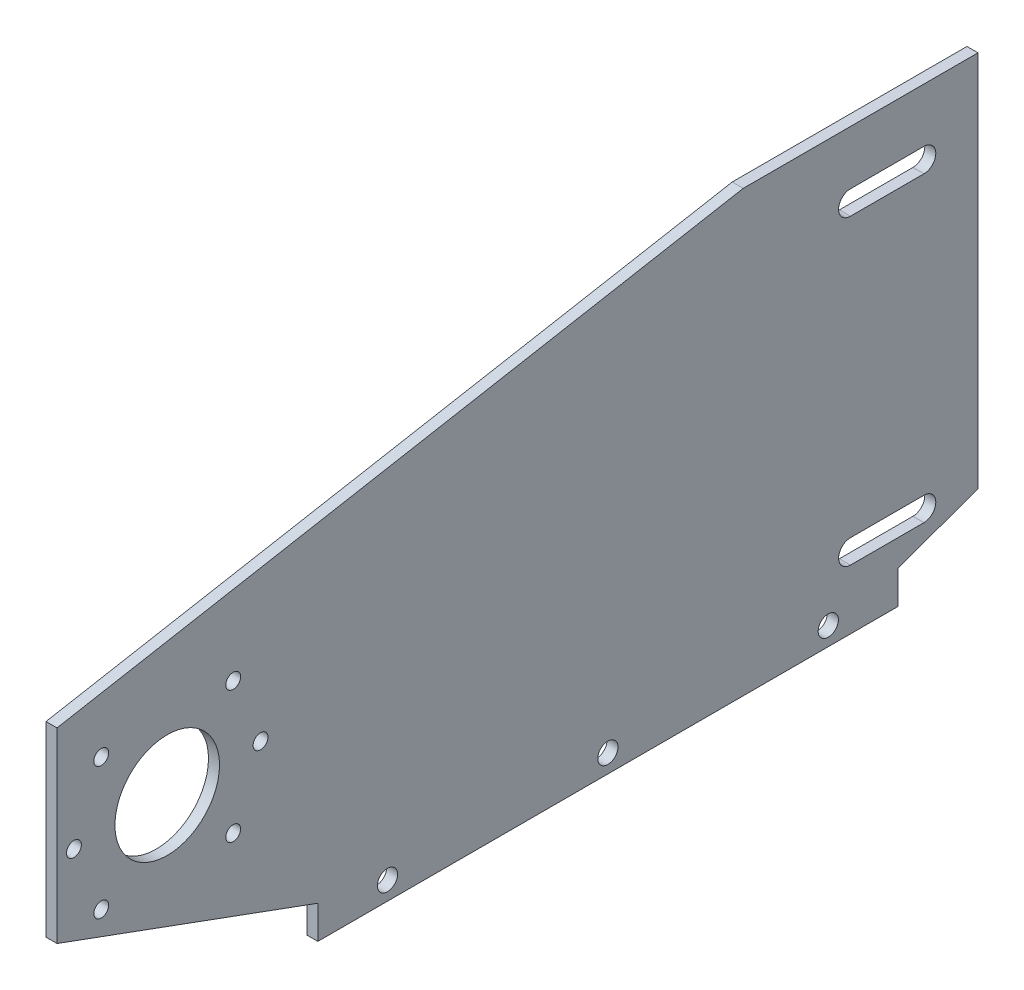
SolidWorks part; units mm, degrees
ref_plane "Front Plane" through (0, 0, 0) normal (0, 0, 1) x (1, 0, 0)
ref_plane "Top Plane" through (0, 0, 0) normal (0, 1, 0) x (1, 0, 0)
ref_plane "Right Plane" through (0, 0, 0) normal (1, 0, 0) x (0, 0, -1)
sketch "Sketch1" plane through (0, 0, 0) normal (1, 0, 0) x (0, 0, -1)
  line L1 (0, 0) -> (300, 0)
  line L2 (0, 0) -> (0, 150)
  line L3 (0, 150) -> (300, 150)
  line L4 (300, 0) -> (300, 150)
  circle A0 centre (30, 55) radius 14.235
  dimension "D1" = 300
  dimension "D5" = 28.47
  dimension "D4" = 55
  dimension "D2" = 150
  dimension "D3" = 30
extrude "Boss-Extrude1" add sketch "Sketch1" along normal blind 3
sketch "Sketch2" plane through (0, 0, 0) normal (-1, 0, 0) x (0, 0, 1)
  line L0 (-236, 104.9384) -> (-216, 104.9384) construction
  line L3 (-216, 98.4784) -> (-236, 98.4784) construction
  line L6 (-216, 16.2317) -> (-236, 16.2317) construction
  line L11 (-236, 22.6817) -> (-216, 22.6817) construction
  line L14 (0, 0) -> (-300, 0) construction
  line L17 (0, 150) -> (0, 0) construction
  line L18 (-236, 104.9384) -> (-216, 104.9384)
  line L19 (-216, 98.4784) -> (-236, 98.4784)
  line L20 (-216, 16.2317) -> (-236, 16.2317)
  line L21 (-236, 22.6817) -> (-216, 22.6817)
  arc A2 (-236, 104.9384) -> (-236, 98.4784) centre (-236, 101.7084) ccw construction
  circle A12 centre (-10, 110) radius 3.225
  arc A14 (-216, 98.4784) -> (-216, 104.9384) centre (-216, 101.7084) ccw construction
  arc A15 (-216, 16.2317) -> (-216, 22.6817) centre (-216, 19.4567) ccw construction
  arc A16 (-236, 22.6817) -> (-236, 16.2317) centre (-236, 19.4567) ccw construction
  arc A17 (-236, 104.9384) -> (-236, 98.4784) centre (-236, 101.7084) ccw
  arc A18 (-216, 98.4784) -> (-216, 104.9384) centre (-216, 101.7084) ccw
  arc A19 (-216, 16.2317) -> (-216, 22.6817) centre (-216, 19.4567) ccw
  arc A20 (-236, 22.6817) -> (-236, 16.2317) centre (-236, 19.4567) ccw
  dimension "D14" = 6.45
  dimension "D20" = 10
  dimension "D21" = 110
extrude "Cut-Extrude1" cut sketch "Sketch2" against normal up to next
sketch "Sketch4" plane through (3, 0, 0) normal (1, 0, 0) x (0, 0, -1)
  line L4 (0, 150) -> (0, 0)
  line L5 (0, 0) -> (300, 0)
  line L6 (300, 0) -> (300, 150)
  line L7 (300, 150) -> (0, 150)
  line L8 (0, 150) -> (0, 0)
  line L9 (0, 0) -> (300, 0)
  line L10 (300, 0) -> (300, 150)
  line L11 (300, 150) -> (0, 150)
  circle A0 centre (47.9605, 37.0395) radius 2.0193 construction
  circle A1 centre (47.9605, 37.0395) radius 2.0193
  circle A2 centre (47.9605, 72.9605) radius 2.0193 construction
  circle A3 centre (47.9605, 72.9605) radius 2.0193
  circle A4 centre (55.4, 55) radius 2.0193 construction
  circle A5 centre (55.4, 55) radius 2.0193
  circle A6 centre (12.0395, 72.9605) radius 2.0193 construction
  circle A7 centre (12.0395, 72.9605) radius 2.0193
  circle A8 centre (4.6, 55) radius 2.0193 construction
  circle A9 centre (4.6, 55) radius 2.0193
  circle A10 centre (12.0395, 37.0395) radius 2.0193 construction
  circle A11 centre (12.0395, 37.0395) radius 2.0193
  dimension "D1" = 0
extrude "Cut-Extrude4" cut sketch "Sketch4" against normal through all contours A11 | A7 | A9 | A1 | A5 | A3
sketch "Sketch5" plane through (0, 0, 0) normal (-1, 0, 0) x (0, 0, 1)
  line L7 (-71, 0) -> (-71, 9) construction
  line L8 (-71, 9) -> (0, 35) construction
  line L9 (-71, 0) -> (-71, 9)
  line L10 (-71, 9) -> (0, 35)
  line L11 (0, 35) -> (0, 0)
  line L12 (0, 0) -> (-71, 0)
  line L13 (0, 85.8486) -> (-186.8026, 119.6415) construction
  line L14 (0, 85.8486) -> (-186.8026, 119.6415)
  line L16 (-300, 150) -> (0, 150) construction
  line L17 (0, 150) -> (0, 85.8486)
  line L19 (-300.3105, 150) -> (0, 150)
  line L20 (-186.8026, 119.6415) -> (-250.718, 119.6415) construction
  line L21 (-186.8026, 119.6415) -> (-300.3105, 119.6415)
  line L22 (-300.3105, 119.6415) -> (-300.3105, 150)
extrude "Cut-Extrude5" cut sketch "Sketch5" against normal through all
sketch "Sketch6" plane through (0, 0, 0) normal (-1, 0, 0) x (0, 0, 1)
  line L8 (-250.718, 150) -> (-250.718, 16.8759) construction
  line L9 (-228.924, 9) -> (-228.924, 0) construction
  line L10 (-250.718, 16.8759) -> (-228.924, 9) construction
  line L11 (-250.718, 165.7129) -> (-250.718, 16.8759)
  line L12 (-228.924, 9) -> (-228.924, 0)
  line L13 (-250.718, 16.8759) -> (-228.924, 9)
  line L14 (-250.718, 165.7129) -> (-364.8309, 165.7129)
  line L15 (-364.8309, 165.7129) -> (-355.7689, 0)
  line L16 (-355.7689, 0) -> (-228.924, 0)
extrude "Cut-Extrude6" cut sketch "Sketch6" against normal blind 10
sketch "Sketch7" plane through (3, 0, 0) normal (1, 0, 0) x (0, 0, -1)
  line L1 (71, 0) -> (228.924, 0) construction
  circle A0 centre (89.962, 5) radius 2.75
  circle A1 centre (149.962, 5) radius 2.75
  circle A2 centre (209.962, 5) radius 2.75
  point P9 (149.962, 0)
  dimension "D1" = 5.5
  dimension "D2" = 5.5
  dimension "D3" = 5.5
  dimension "D4" = 60
  dimension "D5" = 60
  dimension "D6" = 5
extrude "Cut-Extrude7" cut sketch "Sketch7" against normal through all
